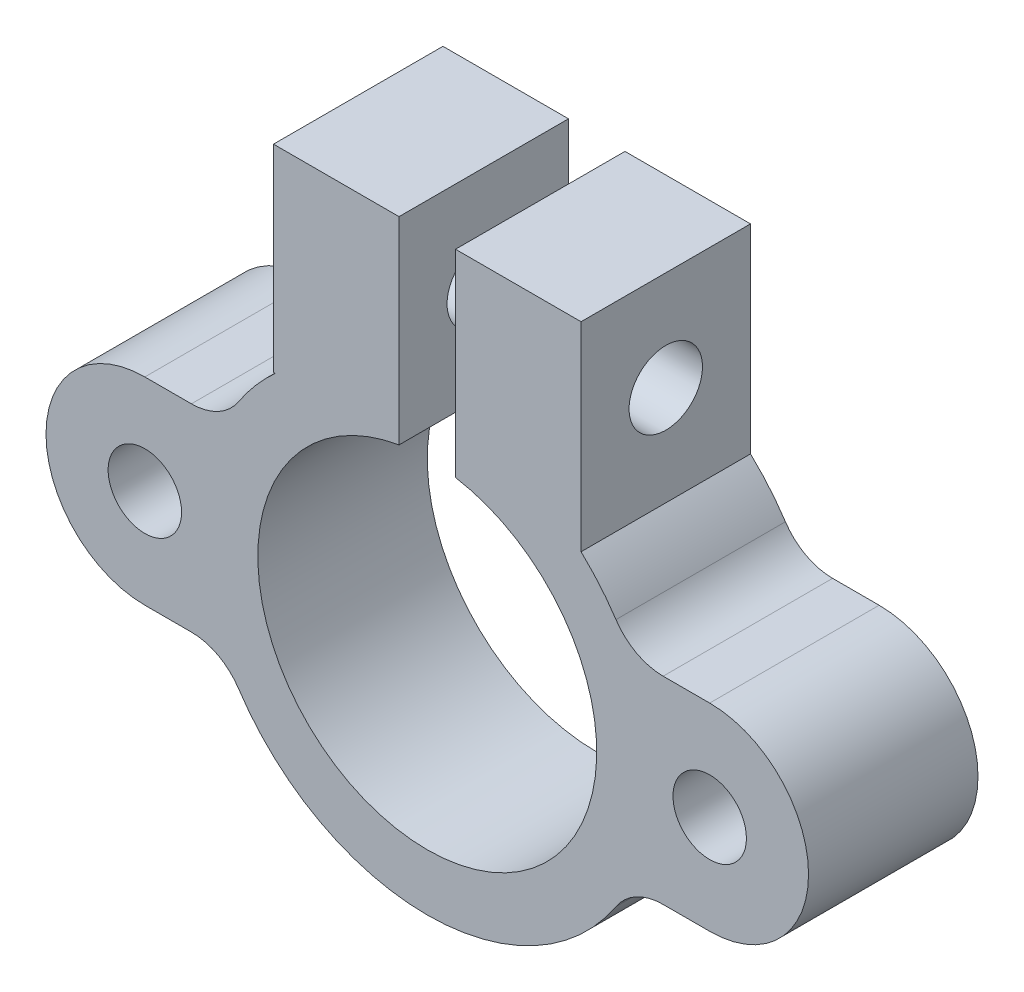
SolidWorks part; units mm, degrees
ref_plane "Front Plane" through (0, 0, 0) normal (0, 0, 1) x (1, 0, 0)
ref_plane "Top Plane" through (0, 0, 0) normal (0, 1, 0) x (1, 0, 0)
ref_plane "Right Plane" through (0, 0, 0) normal (1, 0, 0) x (0, 0, -1)
sketch "Sketch1" plane through (0, 0, 0) normal (0, 0, 1) x (1, 0, 0)
  line L0 (-10, 0) -> (10, 0) construction
  line L1 (-10, 3.5) -> (-8.3516, 3.5)
  line L2 (-10, -3.5) -> (-8.3516, -3.5)
  line L3 (8.3516, 3.5) -> (10, 3.5)
  line L4 (8.3516, -3.5) -> (10, -3.5)
  line L5 (-1, 12.9161) -> (-1, 5.9161)
  line L6 (-5.3852, 5.9161) -> (-5.4448, 5.9161)
  line L7 (0, 0) -> (0, -8) construction
  line L8 (1, 12.9161) -> (1, 5.9161)
  line L9 (1, 12.9161) -> (5.4448, 12.9161)
  line L10 (-1, 12.9161) -> (-5.4448, 12.9161)
  line L11 (-5.4448, 5.9161) -> (-5.4448, 12.9161)
  line L12 (5.4448, 12.9161) -> (5.4448, 5.8613)
  arc A0 (-1, 5.9161) -> (1, 5.9161) centre (0, 0) ccw
  arc A1 (-6.6813, -4.4) -> (6.6813, -4.4) centre (0, 0) ccw
  circle A2 centre (-10, 0) radius 1.3
  circle A3 centre (10, 0) radius 1.3
  arc A4 (-10, 3.5) -> (-10, -3.5) centre (-10, 0) ccw
  arc A5 (10, -3.5) -> (10, 3.5) centre (10, 0) ccw
  arc A6 (6.6813, 4.4) -> (5.4448, 5.8613) centre (0, 0) ccw
  arc A7 (-5.3852, 5.9161) -> (-6.6813, 4.4) centre (0, 0) ccw
  arc A8 (6.6813, 4.4) -> (8.3516, 3.5) centre (8.3516, 5.5) ccw
  arc A9 (8.3516, -3.5) -> (6.6813, -4.4) centre (8.3516, -5.5) ccw
  arc A10 (-6.6813, -4.4) -> (-8.3516, -3.5) centre (-8.3516, -5.5) ccw
  arc A11 (-6.6813, 4.4) -> (-8.3516, 3.5) centre (-8.3516, 5.5) cw
  point P9 (0, 0)
  point P28 (7.1937, 3.5)
  point P31 (7.1937, -3.5)
  dimension "D1" = 7
  dimension "D2" = 2
extrude "Boss-Extrude1" add sketch "Sketch1" along normal blind 6
sketch "Sketch2" plane through (5.4448, 0, 0) normal (1, 0, 0) x (0, 0, -1)
  line L0 (-3, 12.9161) -> (-3, 5.8613) construction
  line L1 (-6, 12.9161) -> (0, 12.9161) construction
  line L2 (-6, 5.8613) -> (0, 5.8613) construction
  circle A0 centre (-3, 9.3887) radius 1.3
extrude "Cut-Extrude1" cut sketch "Sketch2" against normal blind 11
